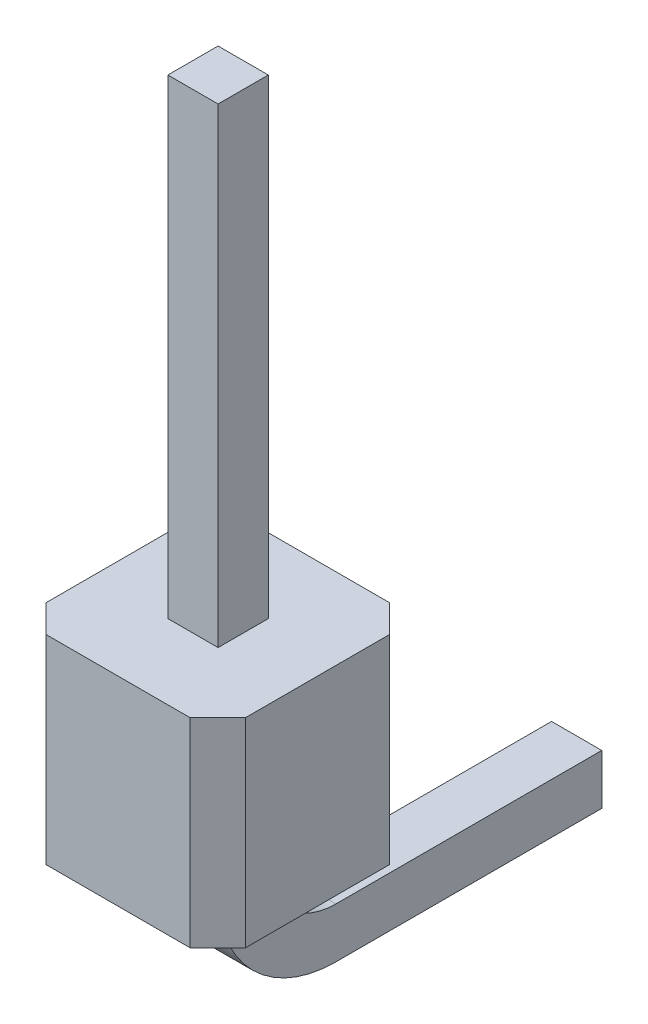
SolidWorks part; units mm, degrees
material "ABS"
ref_plane "Front Plane" through (0, 0, 0) normal (0, 0, 1) x (1, 0, 0)
ref_plane "Top Plane" through (0, 0, 0) normal (0, 1, 0) x (1, 0, 0)
ref_plane "Right Plane" through (0, 0, 0) normal (1, 0, 0) x (0, 0, -1)
sketch "Sketch1" plane through (0, 0, 0) normal (0, -1, 0) x (1, 0, 0)
  line L0 (-0.952, -1.2344) -> (-1.588, -1.2344)
  line L1 (-1.588, -1.2344) -> (-1.588, -0.5984)
  line L2 (-1.588, -0.5984) -> (-0.952, -0.5984)
  line L3 (-0.952, -0.5984) -> (-0.952, -1.2344)
  line L4 (-0.3536, -2.1864) -> (-2.1864, -2.1864)
  line L5 (-2.1864, 0.3536) -> (-2.1864, -2.1864) construction
  line L6 (-1.27, -0.5984) -> (-1.27, 0.3536) construction
  line L15 (-0.3536, -2.1864) -> (-2.1864, -2.1864) construction
  line L17 (-0.952, -0.9164) -> (0, -0.9164) construction
  line L54 (-0.3536, -2.1864) -> (0, -1.8329)
  line L56 (0, 0) -> (-0.3536, 0.3536)
  line L57 (-0.3536, 0.3536) -> (-2.1864, 0.3536)
  line L58 (-2.1864, 0.3536) -> (-2.54, 0)
  line L59 (-2.54, 0) -> (-2.54, -1.8329)
  line L60 (-2.54, -1.8329) -> (-2.1864, -2.1864)
  line L323 (0, 0) -> (0, -1.8329)
  line L563 (-0.952, -3.7744) -> (-1.588, -3.7744) [skipped]
  line L564 (-1.588, -3.7744) -> (-1.588, -3.1384) [skipped]
  line L565 (-1.588, -3.1384) -> (-0.952, -3.1384) [skipped]
  line L566 (-0.952, -3.1384) -> (-0.952, -3.7744) [skipped]
  line L567 (-2.1864, -2.1864) -> (-2.54, -2.54) [skipped]
  line L568 (-2.54, -2.54) -> (-2.54, -4.3729) [skipped]
  line L569 (-2.54, -4.3729) -> (-2.1864, -4.7264) [skipped]
  line L570 (-0.952, -6.3144) -> (-1.588, -6.3144) [skipped]
  line L571 (-1.588, -6.3144) -> (-1.588, -5.6784) [skipped]
  line L572 (-1.588, -5.6784) -> (-0.952, -5.6784) [skipped]
  line L573 (-0.952, -5.6784) -> (-0.952, -6.3144) [skipped]
  line L574 (-2.1864, -4.7264) -> (-2.54, -5.08) [skipped]
  line L575 (-2.54, -5.08) -> (-2.54, -6.9129) [skipped]
  line L576 (-2.54, -6.9129) -> (-2.1864, -7.2664) [skipped]
  line L577 (-0.952, -8.8544) -> (-1.588, -8.8544) [skipped]
  line L578 (-1.588, -8.8544) -> (-1.588, -8.2184) [skipped]
  line L579 (-1.588, -8.2184) -> (-0.952, -8.2184) [skipped]
  line L580 (-0.952, -8.2184) -> (-0.952, -8.8544) [skipped]
  line L581 (-2.1864, -7.2664) -> (-2.54, -7.62) [skipped]
  line L582 (-2.54, -7.62) -> (-2.54, -9.4529) [skipped]
  line L583 (-2.54, -9.4529) -> (-2.1864, -9.8064) [skipped]
  line L584 (-0.952, -11.3944) -> (-1.588, -11.3944) [skipped]
  line L585 (-1.588, -11.3944) -> (-1.588, -10.7584) [skipped]
  line L586 (-1.588, -10.7584) -> (-0.952, -10.7584) [skipped]
  line L587 (-0.952, -10.7584) -> (-0.952, -11.3944) [skipped]
  line L588 (-2.1864, -9.8064) -> (-2.54, -10.16) [skipped]
  line L589 (-2.54, -10.16) -> (-2.54, -11.9929) [skipped]
  line L590 (-2.54, -11.9929) -> (-2.1864, -12.3464) [skipped]
  line L591 (-0.952, -13.9344) -> (-1.588, -13.9344) [skipped]
  line L592 (-1.588, -13.9344) -> (-1.588, -13.2984) [skipped]
  line L593 (-1.588, -13.2984) -> (-0.952, -13.2984) [skipped]
  line L594 (-0.952, -13.2984) -> (-0.952, -13.9344) [skipped]
  line L595 (-2.1864, -12.3464) -> (-2.54, -12.7) [skipped]
  line L596 (-2.54, -12.7) -> (-2.54, -14.5329) [skipped]
  line L597 (-2.54, -14.5329) -> (-2.1864, -14.8864) [skipped]
  line L598 (-2.1864, -14.8864) -> (-2.54, -15.24) [skipped]
  line L615 (-0.3536, -4.7264) -> (-2.1864, -4.7264) construction
  line L616 (-0.3536, -4.7264) -> (0, -4.3729) construction
  line L618 (0, -2.54) -> (-0.3536, -2.1864) construction
  line L620 (-1.27, -3.1384) -> (-1.27, -2.1864) construction
  line L621 (-0.3536, -7.2664) -> (-2.1864, -7.2664) construction
  line L622 (-0.3536, -7.2664) -> (0, -6.9129) construction
  line L624 (0, -5.08) -> (-0.3536, -4.7264) construction
  line L625 (-0.3536, -4.7264) -> (-2.1864, -4.7264) construction
  line L627 (-1.27, -5.6784) -> (-1.27, -4.7264) construction
  line L628 (-0.3536, -9.8064) -> (-2.1864, -9.8064) construction
  line L629 (-0.3536, -9.8064) -> (0, -9.4529) construction
  line L631 (0, -7.62) -> (-0.3536, -7.2664) construction
  line L632 (-0.3536, -7.2664) -> (-2.1864, -7.2664) construction
  line L634 (-1.27, -8.2184) -> (-1.27, -7.2664) construction
  line L635 (-0.3536, -12.3464) -> (-2.1864, -12.3464) construction
  line L636 (-0.3536, -12.3464) -> (0, -11.9929) construction
  line L638 (0, -10.16) -> (-0.3536, -9.8064) construction
  line L639 (-0.3536, -9.8064) -> (-2.1864, -9.8064) construction
  line L641 (-1.27, -10.7584) -> (-1.27, -9.8064) construction
  line L642 (-0.3536, -14.8864) -> (-2.1864, -14.8864) construction
  line L643 (-0.3536, -14.8864) -> (0, -14.5329) construction
  line L645 (0, -12.7) -> (-0.3536, -12.3464) construction
  line L646 (-0.3536, -12.3464) -> (-2.1864, -12.3464) construction
  line L648 (-1.27, -13.2984) -> (-1.27, -12.3464) construction
  line L649 (0, -15.24) -> (-0.3536, -14.8864) construction
  line L650 (-0.3536, -14.8864) -> (-2.1864, -14.8864) construction
  line L651 (-1.27, -15.8384) -> (-1.27, -14.8864) construction
  line L652 (-0.952, -16.4744) -> (-1.588, -16.4744) [skipped]
  line L653 (-1.588, -16.4744) -> (-1.588, -15.8384) [skipped]
  line L654 (-1.588, -15.8384) -> (-0.952, -15.8384) [skipped]
  line L655 (-0.952, -15.8384) -> (-0.952, -16.4744) [skipped]
  line L656 (-2.54, -15.24) -> (-2.54, -17.0729) [skipped]
  line L657 (-2.54, -17.0729) -> (-2.1864, -17.4264) [skipped]
  line L658 (-0.952, -19.0144) -> (-1.588, -19.0144) [skipped]
  line L659 (-1.588, -19.0144) -> (-1.588, -18.3784) [skipped]
  line L660 (-1.588, -18.3784) -> (-0.952, -18.3784) [skipped]
  line L661 (-0.952, -18.3784) -> (-0.952, -19.0144) [skipped]
  line L662 (-2.1864, -17.4264) -> (-2.54, -17.78) [skipped]
  line L663 (-2.54, -17.78) -> (-2.54, -19.6129) [skipped]
  line L664 (-2.54, -19.6129) -> (-2.1864, -19.9664) [skipped]
  line L665 (-0.952, -21.5544) -> (-1.588, -21.5544) [skipped]
  line L666 (-1.588, -21.5544) -> (-1.588, -20.9184) [skipped]
  line L667 (-1.588, -20.9184) -> (-0.952, -20.9184) [skipped]
  line L668 (-0.952, -20.9184) -> (-0.952, -21.5544) [skipped]
  line L669 (-2.1864, -19.9664) -> (-2.54, -20.32) [skipped]
  line L670 (-2.54, -20.32) -> (-2.54, -22.1529) [skipped]
  line L671 (-2.54, -22.1529) -> (-2.1864, -22.5064) [skipped]
  line L672 (-0.952, -24.0944) -> (-1.588, -24.0944) [skipped]
  line L673 (-1.588, -24.0944) -> (-1.588, -23.4584) [skipped]
  line L674 (-1.588, -23.4584) -> (-0.952, -23.4584) [skipped]
  line L675 (-0.952, -23.4584) -> (-0.952, -24.0944) [skipped]
  line L676 (-2.1864, -22.5064) -> (-2.54, -22.86) [skipped]
  line L677 (-2.54, -22.86) -> (-2.54, -24.6929) [skipped]
  line L678 (-2.54, -24.6929) -> (-2.1864, -25.0464) [skipped]
  line L679 (-0.952, -26.6344) -> (-1.588, -26.6344) [skipped]
  line L680 (-1.588, -26.6344) -> (-1.588, -25.9984) [skipped]
  line L681 (-1.588, -25.9984) -> (-0.952, -25.9984) [skipped]
  line L682 (-0.952, -25.9984) -> (-0.952, -26.6344) [skipped]
  line L683 (-2.1864, -25.0464) -> (-2.54, -25.4) [skipped]
  line L684 (-2.54, -25.4) -> (-2.54, -27.2329) [skipped]
  line L685 (-2.54, -27.2329) -> (-2.1864, -27.5864) [skipped]
  line L686 (-0.952, -29.1744) -> (-1.588, -29.1744) [skipped]
  line L687 (-1.588, -29.1744) -> (-1.588, -28.5384) [skipped]
  line L688 (-1.588, -28.5384) -> (-0.952, -28.5384) [skipped]
  line L689 (-0.952, -28.5384) -> (-0.952, -29.1744) [skipped]
  line L690 (-2.1864, -27.5864) -> (-2.54, -27.94) [skipped]
  line L691 (-2.54, -27.94) -> (-2.54, -29.7729) [skipped]
  line L692 (-2.54, -29.7729) -> (-2.1864, -30.1264) [skipped]
  line L693 (-0.952, -31.7144) -> (-1.588, -31.7144) [skipped]
  line L694 (-1.588, -31.7144) -> (-1.588, -31.0784) [skipped]
  line L695 (-1.588, -31.0784) -> (-0.952, -31.0784) [skipped]
  line L696 (-0.952, -31.0784) -> (-0.952, -31.7144) [skipped]
  line L697 (-2.1864, -30.1264) -> (-2.54, -30.48) [skipped]
  line L698 (-2.54, -30.48) -> (-2.54, -32.3129) [skipped]
  line L699 (-2.54, -32.3129) -> (-2.1864, -32.6664) [skipped]
  line L700 (-0.952, -34.2544) -> (-1.588, -34.2544) [skipped]
  line L701 (-1.588, -34.2544) -> (-1.588, -33.6184) [skipped]
  line L702 (-1.588, -33.6184) -> (-0.952, -33.6184) [skipped]
  line L703 (-0.952, -33.6184) -> (-0.952, -34.2544) [skipped]
  line L704 (-2.1864, -32.6664) -> (-2.54, -33.02) [skipped]
  line L705 (-2.54, -33.02) -> (-2.54, -34.8529) [skipped]
  line L706 (-2.54, -34.8529) -> (-2.1864, -35.2064) [skipped]
  line L707 (-0.952, -36.7944) -> (-1.588, -36.7944) [skipped]
  line L708 (-1.588, -36.7944) -> (-1.588, -36.1584) [skipped]
  line L709 (-1.588, -36.1584) -> (-0.952, -36.1584) [skipped]
  line L710 (-0.952, -36.1584) -> (-0.952, -36.7944) [skipped]
  line L711 (-2.1864, -35.2064) -> (-2.54, -35.56) [skipped]
  line L712 (-2.54, -35.56) -> (-2.54, -37.3929) [skipped]
  line L713 (-2.54, -37.3929) -> (-2.1864, -37.7464) [skipped]
  line L714 (-0.952, -39.3344) -> (-1.588, -39.3344) [skipped]
  line L715 (-1.588, -39.3344) -> (-1.588, -38.6984) [skipped]
  line L716 (-1.588, -38.6984) -> (-0.952, -38.6984) [skipped]
  line L717 (-0.952, -38.6984) -> (-0.952, -39.3344) [skipped]
  line L718 (-2.1864, -37.7464) -> (-2.54, -38.1) [skipped]
  line L719 (-2.54, -38.1) -> (-2.54, -39.9329) [skipped]
  line L720 (-2.54, -39.9329) -> (-2.1864, -40.2864) [skipped]
  line L721 (-0.952, -41.8744) -> (-1.588, -41.8744) [skipped]
  line L722 (-1.588, -41.8744) -> (-1.588, -41.2384) [skipped]
  line L723 (-1.588, -41.2384) -> (-0.952, -41.2384) [skipped]
  line L724 (-0.952, -41.2384) -> (-0.952, -41.8744) [skipped]
  line L725 (-2.1864, -40.2864) -> (-2.54, -40.64) [skipped]
  line L726 (-2.54, -40.64) -> (-2.54, -42.4729) [skipped]
  line L727 (-2.54, -42.4729) -> (-2.1864, -42.8264) [skipped]
  line L728 (-0.952, -44.4144) -> (-1.588, -44.4144) [skipped]
  line L729 (-1.588, -44.4144) -> (-1.588, -43.7784) [skipped]
  line L730 (-1.588, -43.7784) -> (-0.952, -43.7784) [skipped]
  line L731 (-0.952, -43.7784) -> (-0.952, -44.4144) [skipped]
  line L732 (-2.1864, -42.8264) -> (-2.54, -43.18) [skipped]
  line L733 (-2.54, -43.18) -> (-2.54, -45.0129) [skipped]
  line L734 (-2.54, -45.0129) -> (-2.1864, -45.3664) [skipped]
  line L735 (-0.952, -46.9544) -> (-1.588, -46.9544) [skipped]
  line L736 (-1.588, -46.9544) -> (-1.588, -46.3184) [skipped]
  line L737 (-1.588, -46.3184) -> (-0.952, -46.3184) [skipped]
  line L738 (-0.952, -46.3184) -> (-0.952, -46.9544) [skipped]
  line L739 (-2.1864, -45.3664) -> (-2.54, -45.72) [skipped]
  line L740 (-2.54, -45.72) -> (-2.54, -47.5529) [skipped]
  line L741 (-2.54, -47.5529) -> (-2.1864, -47.9064) [skipped]
  line L742 (-0.952, -49.4944) -> (-1.588, -49.4944) [skipped]
  line L743 (-1.588, -49.4944) -> (-1.588, -48.8584) [skipped]
  line L744 (-1.588, -48.8584) -> (-0.952, -48.8584) [skipped]
  line L745 (-0.952, -48.8584) -> (-0.952, -49.4944) [skipped]
  line L746 (-2.1864, -47.9064) -> (-2.54, -48.26) [skipped]
  line L747 (-2.54, -48.26) -> (-2.54, -50.0929) [skipped]
  line L748 (-2.54, -50.0929) -> (-2.1864, -50.4464) [skipped]
  line L790 (-0.3536, -17.4264) -> (-2.1864, -17.4264) construction
  line L791 (-0.3536, -17.4264) -> (0, -17.0729) construction
  line L794 (-0.3536, -19.9664) -> (-2.1864, -19.9664) construction
  line L795 (-0.3536, -19.9664) -> (0, -19.6129) construction
  line L797 (0, -17.78) -> (-0.3536, -17.4264) construction
  line L798 (-0.3536, -17.4264) -> (-2.1864, -17.4264) construction
  line L800 (-1.27, -18.3784) -> (-1.27, -17.4264) construction
  line L801 (-0.3536, -22.5064) -> (-2.1864, -22.5064) construction
  line L802 (-0.3536, -22.5064) -> (0, -22.1529) construction
  line L804 (0, -20.32) -> (-0.3536, -19.9664) construction
  line L805 (-0.3536, -19.9664) -> (-2.1864, -19.9664) construction
  line L807 (-1.27, -20.9184) -> (-1.27, -19.9664) construction
  line L808 (-0.3536, -25.0464) -> (-2.1864, -25.0464) construction
  line L809 (-0.3536, -25.0464) -> (0, -24.6929) construction
  line L811 (0, -22.86) -> (-0.3536, -22.5064) construction
  line L812 (-0.3536, -22.5064) -> (-2.1864, -22.5064) construction
  line L814 (-1.27, -23.4584) -> (-1.27, -22.5064) construction
  line L815 (-0.3536, -27.5864) -> (-2.1864, -27.5864) construction
  line L816 (-0.3536, -27.5864) -> (0, -27.2329) construction
  line L818 (0, -25.4) -> (-0.3536, -25.0464) construction
  line L819 (-0.3536, -25.0464) -> (-2.1864, -25.0464) construction
  line L821 (-1.27, -25.9984) -> (-1.27, -25.0464) construction
  line L822 (-0.3536, -30.1264) -> (-2.1864, -30.1264) construction
  line L823 (-0.3536, -30.1264) -> (0, -29.7729) construction
  line L825 (0, -27.94) -> (-0.3536, -27.5864) construction
  line L826 (-0.3536, -27.5864) -> (-2.1864, -27.5864) construction
  line L828 (-1.27, -28.5384) -> (-1.27, -27.5864) construction
  line L829 (-0.3536, -32.6664) -> (-2.1864, -32.6664) construction
  line L830 (-0.3536, -32.6664) -> (0, -32.3129) construction
  line L832 (0, -30.48) -> (-0.3536, -30.1264) construction
  line L833 (-0.3536, -30.1264) -> (-2.1864, -30.1264) construction
  line L835 (-1.27, -31.0784) -> (-1.27, -30.1264) construction
  line L836 (-0.3536, -35.2064) -> (-2.1864, -35.2064) construction
  line L837 (-0.3536, -35.2064) -> (0, -34.8529) construction
  line L839 (0, -33.02) -> (-0.3536, -32.6664) construction
  line L840 (-0.3536, -32.6664) -> (-2.1864, -32.6664) construction
  line L842 (-1.27, -33.6184) -> (-1.27, -32.6664) construction
  line L843 (-0.3536, -37.7464) -> (-2.1864, -37.7464) construction
  line L844 (-0.3536, -37.7464) -> (0, -37.3929) construction
  line L846 (0, -35.56) -> (-0.3536, -35.2064) construction
  line L847 (-0.3536, -35.2064) -> (-2.1864, -35.2064) construction
  line L849 (-1.27, -36.1584) -> (-1.27, -35.2064) construction
  line L850 (-0.3536, -40.2864) -> (-2.1864, -40.2864) construction
  line L851 (-0.3536, -40.2864) -> (0, -39.9329) construction
  line L853 (0, -38.1) -> (-0.3536, -37.7464) construction
  line L854 (-0.3536, -37.7464) -> (-2.1864, -37.7464) construction
  line L856 (-1.27, -38.6984) -> (-1.27, -37.7464) construction
  line L857 (-0.3536, -42.8264) -> (-2.1864, -42.8264) construction
  line L858 (-0.3536, -42.8264) -> (0, -42.4729) construction
  line L860 (0, -40.64) -> (-0.3536, -40.2864) construction
  line L861 (-0.3536, -40.2864) -> (-2.1864, -40.2864) construction
  line L863 (-1.27, -41.2384) -> (-1.27, -40.2864) construction
  line L864 (-0.3536, -45.3664) -> (-2.1864, -45.3664) construction
  line L865 (-0.3536, -45.3664) -> (0, -45.0129) construction
  line L867 (0, -43.18) -> (-0.3536, -42.8264) construction
  line L868 (-0.3536, -42.8264) -> (-2.1864, -42.8264) construction
  line L870 (-1.27, -43.7784) -> (-1.27, -42.8264) construction
  line L871 (-0.3536, -47.9064) -> (-2.1864, -47.9064) construction
  line L872 (-0.3536, -47.9064) -> (0, -47.5529) construction
  line L874 (0, -45.72) -> (-0.3536, -45.3664) construction
  line L875 (-0.3536, -45.3664) -> (-2.1864, -45.3664) construction
  line L877 (-1.27, -46.3184) -> (-1.27, -45.3664) construction
  line L878 (-0.3536, -50.4464) -> (-2.1864, -50.4464) construction
  line L879 (-0.3536, -50.4464) -> (0, -50.0929) construction
  line L881 (0, -48.26) -> (-0.3536, -47.9064) construction
  line L882 (-0.3536, -47.9064) -> (-2.1864, -47.9064) construction
  line L884 (-1.27, -48.8584) -> (-1.27, -47.9064) construction
  line L885 (2.1864, 0.3536) -> (0.3536, 0.3536) construction
  line L886 (1.588, -1.2344) -> (0.952, -1.2344) [skipped]
  line L887 (0.952, -1.2344) -> (0.952, -0.5984) [skipped]
  line L888 (0.952, -0.5984) -> (1.588, -0.5984) [skipped]
  line L889 (1.588, -0.5984) -> (1.588, -1.2344) [skipped]
  line L890 (2.1864, -2.1864) -> (16.4995, 12.1266) [skipped]
  line L891 (-9.9832, 12.5232) -> (2.1864, 0.3536) [skipped]
  line L892 (2.1864, -2.1864) -> (0.3536, -2.1864) construction
  line L894 (1.27, -0.5984) -> (1.27, 0.3536) construction
  line L895 (2.1864, -2.1864) -> (0.3536, -2.1864) construction
  line L897 (0, -1.8329) -> (0.3536, -2.1864) construction
  line L898 (0.3536, 0.3536) -> (0, 0) construction
  dimension "D1" = 0.636
  dimension "D7" = 0.5
  dimension "D3" = 45
  dimension "D4" = 2.54
  dimension "D6" = 2.54
  dimension "D2" = 20
  dimension "D8" = 2
extrude "Boss-Extrude1" add sketch "Sketch1" against normal blind 2.54
sketch "Esquisse1" plane through (-1.588, 0, 0) normal (1, 0, 0) x (0, 0, -1)
  line L0 (0.5984, 8.54) -> (0.5984, -0.18)
  line L1 (1.2384, -0.18) -> (1.2384, 8.54)
  line L2 (1.2384, 8.54) -> (0.5984, 8.54)
  line L3 (2.0984, -1.04) -> (5.4884, -1.04)
  line L4 (5.4884, -1.04) -> (5.4884, -1.68)
  line L5 (5.4884, -1.68) -> (2.0984, -1.68)
  arc A0 (0.5984, -0.18) -> (2.0984, -1.68) centre (2.0984, -0.18) ccw
  arc A1 (2.0984, -1.04) -> (1.2384, -0.18) centre (2.0984, -0.18) cw
  point P0 (0.5984, 2.54)
  point P6 (0.5984, 2.54)
  point P11 (0.5984, 2.54)
  point P13 (0.5984, 5.363)
  point P14 (0.5984, 4.5366)
  point P15 (2.0984, -2.7171)
  dimension "D2" = 1.5
  dimension "D1" = 0.64
  dimension "D3" = 4.89
  dimension "D4" = 10.22
  dimension "D5" = 6
extrude "Boss.-Extru.1" add sketch "Esquisse1" along normal blind 0.64
equation "\"D1@Boss-Extrude1\"= \"D4@Sketch1\""
equation "\"D6@Sketch1\"=\"D4@Sketch1\""
